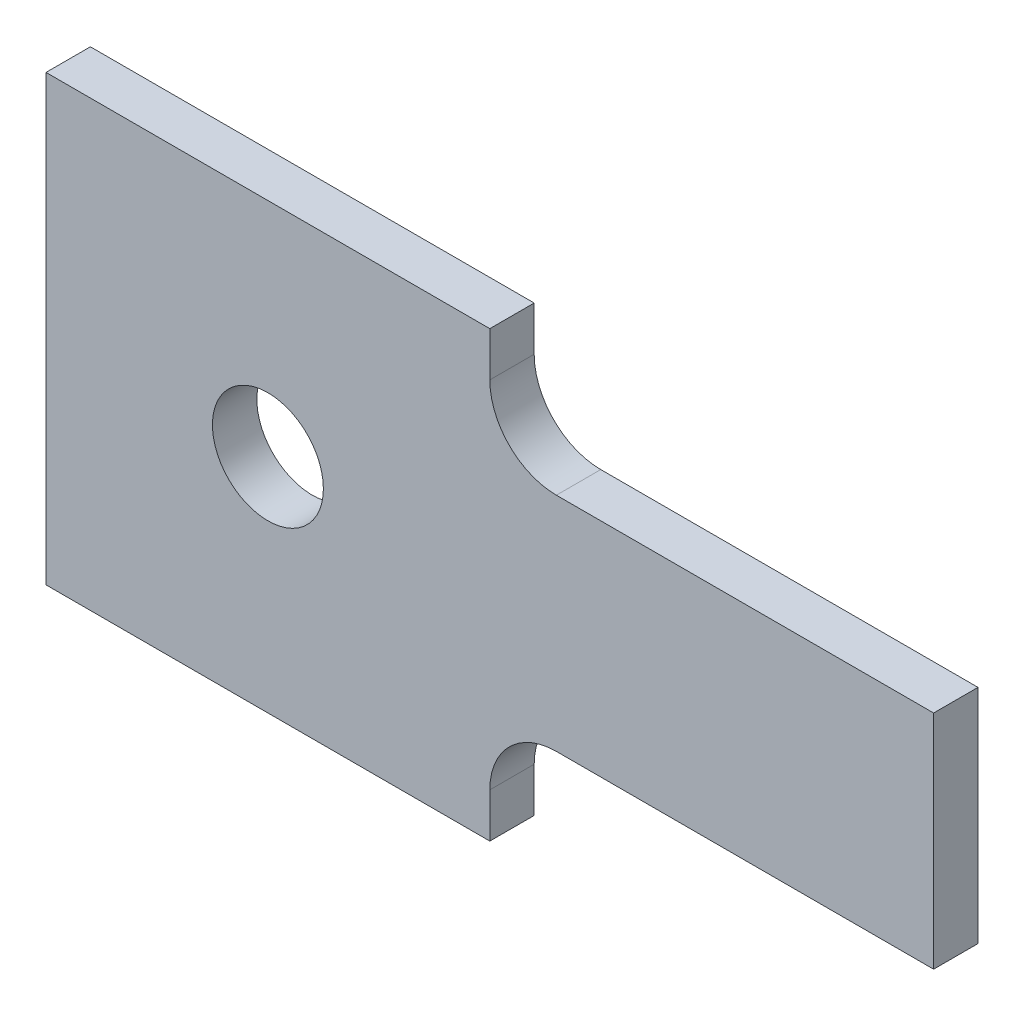
SolidWorks part; units mm, degrees
ref_plane "Front Plane" through (0, 0, 0) normal (0, 0, 1) x (1, 0, 0)
ref_plane "Top Plane" through (0, 0, 0) normal (0, 1, 0) x (1, 0, 0)
ref_plane "Right Plane" through (0, 0, 0) normal (1, 0, 0) x (0, 0, -1)
sketch "Sketch1" plane through (0, 0, 0) normal (0, 0, 1) x (1, 0, 0)
  line L0 (0, 0) -> (200, 0) construction
  line L1 (200, -25) -> (200, 25)
  line L2 (200, 25) -> (115, 25)
  line L3 (100, 40) -> (100, 50)
  line L4 (100, 50) -> (0, 50)
  line L5 (0, 50) -> (0, -50)
  line L6 (100, -50) -> (0, -50)
  line L7 (100, -40) -> (100, -50)
  line L8 (200, -25) -> (115, -25)
  arc A0 (115, 25) -> (100, 40) centre (115, 40) cw
  arc A1 (115, -25) -> (100, -40) centre (115, -40) ccw
  dimension "D5" = 15
  dimension "D1" = 25
  dimension "D2" = 50
  dimension "D3" = 100
  dimension "D4" = 100
extrude "Boss-Extrude1" add sketch "Sketch1" along normal blind 10
sketch "Sketch2" plane through (0, 0, 10) normal (0, 0, 1) x (1, 0, 0)
  circle A0 centre (50, 0) radius 12.5
  dimension "D1" = 25
extrude "Cut-Extrude1" cut sketch "Sketch2" against normal through all
sketch "Sketch3" plane through (0, 0, 0) normal (-1, 0, 0) x (0, 0, 1)
  line L0 (0, 0) -> (10, 0)
  line L1 (10, 50) -> (10, -50) construction
  line L2 (5, 50) -> (5, -50)
  line L3 (10, 50) -> (0, 50) construction
  line L4 (10, -50) -> (0, -50) construction
split line "Split Line1"
